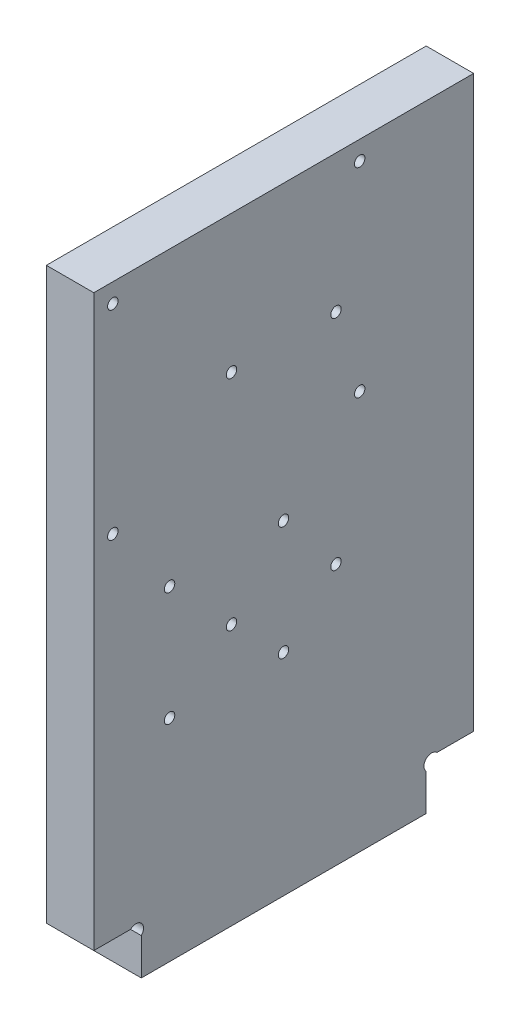
SolidWorks part; units mm, degrees
ref_plane "Plan de face" through (0, 0, 0) normal (0, 0, 1) x (1, 0, 0)
ref_plane "Plan de dessus" through (0, 0, 0) normal (0, 1, 0) x (1, 0, 0)
ref_plane "Plan de droite" through (0, 0, 0) normal (1, 0, 0) x (0, 0, -1)
sketch "Esquisse1" plane through (0, 0, 0) normal (1, 0, 0) x (0, 0, -1)
  line L0 (-8.8502, 0) -> (128.8987, 0) construction
  line L1 (0, -8.3785) -> (0, 173.327) construction
  line L2 (80, -8.3785) -> (80, 173.327) construction
  line L3 (-8.8502, 130) -> (128.8987, 130) construction
  line L4 (-8.8502, 10) -> (84.0299, 10) construction
  line L5 (40, 158.0773) -> (40, -8.3785) construction
  line L6 (10, 25.7788) -> (10, -8.3785) construction
  line L7 (10, 10) -> (-12.9167, -12.9167) construction
  line L8 (10, 7.7373) -> (10, 0)
  line L9 (70, 7.7373) -> (70, 0)
  line L10 (7.7373, 10) -> (0, 10)
  line L11 (10, 0) -> (70, 0)
  line L12 (72.2627, 10) -> (80, 10)
  line L13 (0, 10) -> (0, 130)
  line L14 (0, 130) -> (80, 130)
  line L15 (80, 130) -> (80, 10)
  line L19 (10, 105) -> (60.653, 105) construction
  line L20 (29, 103.2629) -> (29, 71.7498) construction
  line L21 (18.0678, 101) -> (37.7989, 101) construction
  line L22 (10, 78) -> (37.7989, 78) construction
  arc A0 (10, 7.7373) -> (7.7373, 10) centre (8.8686, 8.8686) ccw
  arc A1 (70, 7.7373) -> (72.2627, 10) centre (71.1314, 8.8686) cw
  circle A6 centre (29, 101) radius 1.1
  circle A7 centre (51, 101) radius 1.1
  circle A8 centre (29, 55) radius 1.1
  circle A9 centre (51, 55) radius 1.1
  dimension "D11" = 27
  dimension "D1" = 80
  dimension "D2" = 40
  dimension "D3" = 130
  dimension "D4" = 10
  dimension "D5" = 10
  dimension "D6" = 45
  dimension "D10" = 25
  dimension "D12" = 4
  dimension "D13" = 29
extrude "Extrusion1" add sketch "Esquisse1" along normal blind 10
sketch "Esquisse2" plane through (10, 0, 0) normal (1, 0, 0) x (0, 0, -1)
  line L0 (-24.0423, 130) -> (94.8043, 130) construction
  line L1 (0, 148.2714) -> (0, -18.6279) construction
  line L2 (-24.0423, 105) -> (46.3515, 105) construction
  line L3 (30, 148.2714) -> (30, 86.0558) construction
  line L4 (-13.0053, 126) -> (8.0236, 126) construction
  line L5 (4, 137.3762) -> (4, 122.9802) construction
  line L6 (-24.0423, 10) -> (109.6003, 10) construction
  line L7 (-24.0423, 68.45) -> (53.0302, 68.45) construction
  line L8 (15.95, 76.3617) -> (15.95, 27.2601) construction
  line L9 (8.0236, 44.45) -> (50.9644, 44.45) construction
  line L10 (39.95, 76.3617) -> (39.95, 30.2793) construction
  circle A0 centre (4, 126) radius 1.1
  circle A1 centre (56, 126) radius 1.1
  circle A2 centre (4, 84) radius 1.1
  circle A3 centre (56, 84) radius 1.1
  circle A4 centre (15.95, 68.45) radius 1.1
  circle A5 centre (15.95, 44.45) radius 1.1
  circle A6 centre (39.95, 44.45) radius 1.1
  circle A7 centre (39.95, 68.45) radius 1.1
  dimension "D5" = 15.95
  dimension "D7" = 24
  dimension "D1" = 4
  dimension "D2" = 4
  dimension "D3" = 25
  dimension "D4" = 30
  dimension "D6" = 58.45
  dimension "D8" = 24
extrude "Enlèv. mat.-Extru.1" cut sketch "Esquisse2" against normal blind 2
